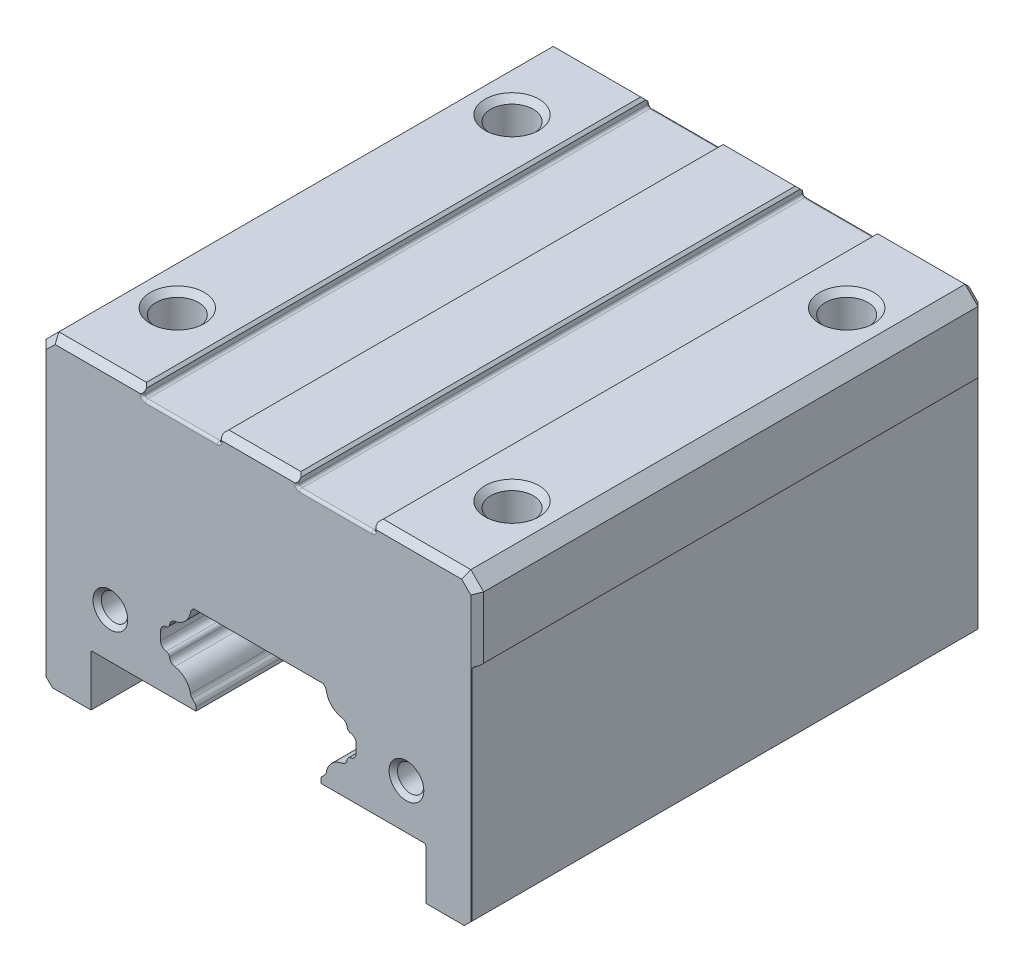
SolidWorks part; units mm, degrees
material "Plain Carbon Steel"
ref_plane "Front Plane" through (0, 0, 0) normal (0, 0, 1) x (1, 0, 0)
ref_plane "Top Plane" through (0, 0, 0) normal (0, 1, 0) x (1, 0, 0)
ref_plane "Right Plane" through (0, 0, 0) normal (1, 0, 0) x (0, 0, -1)
sketch "Rail Profile" plane through (0, 0, 0) normal (0, 0, 1) x (1, 0, 0)
  line L47 (0, 0) -> (0, 28) construction
  line L48 (-7, 0) -> (7, 0)
  line L49 (7, 0) -> (7.5, 0.5)
  line L50 (7.5, 0.5) -> (7.5, 3.0858)
  line L58 (7.2071, 3.7929) -> (4.8672, 6.1328)
  line L59 (4.75, 6.4157) -> (4.75, 8.5843)
  line L60 (4.8672, 8.8672) -> (5.063, 9.063)
  line L61 (7.5, 11.6657) -> (7.5, 12.3343)
  line L62 (-7, 0) -> (-7.5, 0.5)
  line L63 (5, 15) -> (-5, 15)
  line L64 (6.75, 9) -> (6.75, 15) construction
  line L65 (5.063, 14.937) -> (5, 15)
  line L66 (-7.5, 0.5) -> (-7.5, 3.0858)
  line L67 (6.75, 15) -> (3.75, 12) construction
  line L68 (3.75, 12) -> (6.75, 9) construction
  line L69 (7.1, 12.3343) -> (7.1, 11.6657) construction
  line L70 (6.4042, 13.0301) -> (6.4042, 10.9699) construction
  line L71 (-7.2071, 3.7929) -> (-4.8672, 6.1328)
  line L72 (-4.75, 6.4157) -> (-4.75, 8.5843)
  line L73 (-4.8672, 8.8672) -> (-5.063, 9.063)
  line L74 (5, 15) -> (8, 12) construction
  line L75 (4.8672, 8.8672) -> (8, 12) construction
  line L76 (-7.5, 11.6657) -> (-7.5, 12.3343)
  line L77 (-5.063, 14.937) -> (-5, 15)
  arc A4 (6.4734, 13.4241) -> (5.1741, 14.7234) centre (6.75, 15) cw
  arc A6 (5.1741, 9.2766) -> (6.4734, 10.5759) centre (6.75, 9) cw
  arc A7 (7.2071, 3.7929) -> (7.5, 3.0858) centre (6.5, 3.0858) cw
  arc A8 (5.063, 14.937) -> (5.1741, 14.7234) centre (4.7801, 14.6542) cw
  arc A9 (6.4734, 13.4241) -> (6.8012, 13.0792) centre (6.4042, 13.0301) cw
  arc A10 (7.1491, 12.7313) -> (7.5, 12.3343) centre (7.1, 12.3343) cw
  arc A11 (7.5, 11.6657) -> (7.1491, 11.2687) centre (7.1, 11.6657) cw
  arc A12 (6.8012, 10.9208) -> (6.4734, 10.5759) centre (6.4042, 10.9699) cw
  arc A13 (5.1741, 9.2766) -> (5.063, 9.063) centre (4.7801, 9.3458) cw
  arc A14 (4.8672, 8.8672) -> (4.75, 8.5843) centre (5.15, 8.5843) ccw
  arc A15 (4.75, 6.4157) -> (4.8672, 6.1328) centre (5.15, 6.4157) ccw
  arc A16 (6.8012, 13.0792) -> (7.1491, 12.7313) centre (7.1981, 13.1283) ccw
  arc A17 (7.1491, 11.2687) -> (6.8012, 10.9208) centre (7.1981, 10.8717) ccw
  arc A18 (-7.2071, 3.7929) -> (-7.5, 3.0858) centre (-6.5, 3.0858) ccw
  arc A19 (-4.75, 6.4157) -> (-4.8672, 6.1328) centre (-5.15, 6.4157) cw
  arc A20 (-4.8672, 8.8672) -> (-4.75, 8.5843) centre (-5.15, 8.5843) cw
  arc A21 (-5.1741, 9.2766) -> (-5.063, 9.063) centre (-4.7801, 9.3458) ccw
  arc A22 (-5.1741, 9.2766) -> (-6.4734, 10.5759) centre (-6.75, 9) ccw
  arc A23 (-6.8012, 10.9208) -> (-6.4734, 10.5759) centre (-6.4042, 10.9699) ccw
  arc A24 (-7.1491, 11.2687) -> (-6.8012, 10.9208) centre (-7.1981, 10.8717) cw
  arc A25 (-7.5, 11.6657) -> (-7.1491, 11.2687) centre (-7.1, 11.6657) ccw
  arc A26 (-7.1491, 12.7313) -> (-7.5, 12.3343) centre (-7.1, 12.3343) ccw
  arc A27 (-6.8012, 13.0792) -> (-7.1491, 12.7313) centre (-7.1981, 13.1283) cw
  arc A28 (-6.4734, 13.4241) -> (-6.8012, 13.0792) centre (-6.4042, 13.0301) ccw
  arc A29 (-6.4734, 13.4241) -> (-5.1741, 14.7234) centre (-6.75, 15) ccw
  arc A30 (-5.063, 14.937) -> (-5.1741, 14.7234) centre (-4.7801, 14.6542) ccw
  point P2 (4.75, 7.5)
  point P12 (7.5, 12)
  point P19 (6.75, 12)
  point P25 (5.1578, 14.8422)
  point P50 (8, 12)
  point P78 (0, 15)
  dimension "Rb" = 1.6
  dimension "Rf1" = 1
  dimension "Rf2" = 0.4
  dimension "WR" = 15
  dimension "Wi" = 9.5
  dimension "Wt" = 5
  dimension "Ac" = 135
  dimension "HR" = 15
  dimension "Hm" = 7.5
  dimension "Hb" = 12
  dimension "Hc" = 0.5
  dimension "Wb" = 7.5
sketch "Block Profile" plane through (0, 0, 0) normal (0, 0, 1) x (1, 0, 0)
  line L16 (16, 4.3) -> (13, 4.3)
  line L17 (0, 0) -> (0, 28) construction
  line L18 (17, 5.3) -> (17, 27)
  line L19 (16, 28) -> (-16, 28)
  line L20 (5.0414, 15.1) -> (-5.0414, 15.1)
  line L21 (0, 15.1) -> (0, 28) construction
  line L22 (17, 5.3) -> (16, 4.3)
  line L23 (17, 27) -> (16, 28)
  line L24 (13, 4.3) -> (13, 8.2)
  line L25 (12.9, 8.3) -> (4.85, 8.3)
  line L26 (-5.1337, 15.0077) -> (-5.0414, 15.1)
  line L27 (-7.6, 11.6657) -> (-7.6, 12.3343)
  line L28 (-4.9379, 8.7964) -> (-5.1337, 8.9923)
  line L29 (-4.85, 8.3) -> (-4.85, 8.5843)
  line L30 (-12.9, 8.3) -> (-4.85, 8.3)
  line L31 (-13, 4.3) -> (-13, 8.2)
  line L32 (5.0414, 15.1) -> (-5.0414, 15.1)
  line L33 (-5.0414, 15.1) -> (-5.1337, 15.0077)
  line L34 (-7.6, 12.3343) -> (-7.6, 11.6657)
  line L35 (-5.1337, 8.9923) -> (-4.9379, 8.7964)
  line L36 (-4.85, 8.5843) -> (-4.85, 6.4157)
  line L37 (-4.9379, 6.2036) -> (-7.2778, 3.8636)
  line L38 (-7.6, 3.0858) -> (-7.6, 0.4586)
  line L39 (-7.6, 0.4586) -> (-7.0414, -0.1)
  line L40 (-7.0414, -0.1) -> (7.0414, -0.1)
  line L41 (7.0414, -0.1) -> (7.6, 0.4586)
  line L42 (7.6, 0.4586) -> (7.6, 3.0858)
  line L43 (7.2778, 3.8636) -> (4.9379, 6.2036)
  line L44 (4.85, 6.4157) -> (4.85, 8.5843)
  line L45 (4.9379, 8.7964) -> (5.1337, 8.9923)
  line L46 (7.6, 11.6657) -> (7.6, 12.3343)
  line L47 (5.1337, 15.0077) -> (5.0414, 15.1)
  line L60 (4.85, 8.3) -> (4.85, 8.5843)
  line L61 (4.9379, 8.7964) -> (5.1337, 8.9923)
  line L62 (7.6, 11.6657) -> (7.6, 12.3343)
  line L63 (5.1337, 15.0077) -> (5.0414, 15.1)
  line L64 (-16, 4.3) -> (-13, 4.3)
  line L65 (-17, 5.3) -> (-16, 4.3)
  line L66 (-17, 5.3) -> (-17, 27)
  line L67 (-17, 27) -> (-16, 28)
  arc A26 (12.9, 8.3) -> (13, 8.2) centre (12.9, 8.2) cw
  arc A27 (-5.2726, 14.7406) -> (-5.1337, 15.0077) centre (-4.7801, 14.6542) cw
  arc A28 (-5.2726, 14.7406) -> (-6.4906, 13.5226) centre (-6.75, 15) cw
  arc A29 (-6.9004, 13.0915) -> (-6.4906, 13.5226) centre (-6.4042, 13.0301) cw
  arc A30 (-6.9004, 13.0915) -> (-7.1613, 12.8305) centre (-7.1981, 13.1283) cw
  arc A31 (-7.6, 12.3343) -> (-7.1613, 12.8305) centre (-7.1, 12.3343) cw
  arc A32 (-7.1613, 11.1695) -> (-7.6, 11.6657) centre (-7.1, 11.6657) cw
  arc A33 (-7.1613, 11.1695) -> (-6.9004, 10.9085) centre (-7.1981, 10.8717) cw
  arc A34 (-6.4906, 10.4774) -> (-6.9004, 10.9085) centre (-6.4042, 10.9699) cw
  arc A35 (-6.4906, 10.4774) -> (-5.2726, 9.2594) centre (-6.75, 9) cw
  arc A36 (-5.1337, 8.9923) -> (-5.2726, 9.2594) centre (-4.7801, 9.3458) cw
  arc A37 (-4.9379, 8.7964) -> (-4.85, 8.5843) centre (-5.15, 8.5843) cw
  arc A38 (-12.9, 8.3) -> (-13, 8.2) centre (-12.9, 8.2) ccw
  arc A52 (-5.1337, 15.0077) -> (-5.2726, 14.7406) centre (-4.7801, 14.6542) ccw
  arc A53 (-6.4906, 13.5226) -> (-5.2726, 14.7406) centre (-6.75, 15) ccw
  arc A54 (-6.4906, 13.5226) -> (-6.9004, 13.0915) centre (-6.4042, 13.0301) ccw
  arc A55 (-7.1613, 12.8305) -> (-6.9004, 13.0915) centre (-7.1981, 13.1283) ccw
  arc A56 (-7.1613, 12.8305) -> (-7.6, 12.3343) centre (-7.1, 12.3343) ccw
  arc A57 (-7.6, 11.6657) -> (-7.1613, 11.1695) centre (-7.1, 11.6657) ccw
  arc A58 (-6.9004, 10.9085) -> (-7.1613, 11.1695) centre (-7.1981, 10.8717) ccw
  arc A59 (-6.9004, 10.9085) -> (-6.4906, 10.4774) centre (-6.4042, 10.9699) ccw
  arc A60 (-5.2726, 9.2594) -> (-6.4906, 10.4774) centre (-6.75, 9) ccw
  arc A61 (-5.2726, 9.2594) -> (-5.1337, 8.9923) centre (-4.7801, 9.3458) ccw
  arc A62 (-4.85, 8.5843) -> (-4.9379, 8.7964) centre (-5.15, 8.5843) ccw
  arc A63 (-4.9379, 6.2036) -> (-4.85, 6.4157) centre (-5.15, 6.4157) ccw
  arc A64 (-7.2778, 3.8636) -> (-7.6, 3.0858) centre (-6.5, 3.0858) ccw
  arc A65 (7.6, 3.0858) -> (7.2778, 3.8636) centre (6.5, 3.0858) ccw
  arc A66 (4.85, 6.4157) -> (4.9379, 6.2036) centre (5.15, 6.4157) ccw
  arc A67 (4.9379, 8.7964) -> (4.85, 8.5843) centre (5.15, 8.5843) ccw
  arc A68 (5.1337, 8.9923) -> (5.2726, 9.2594) centre (4.7801, 9.3458) ccw
  arc A69 (6.4906, 10.4774) -> (5.2726, 9.2594) centre (6.75, 9) ccw
  arc A70 (6.4906, 10.4774) -> (6.9004, 10.9085) centre (6.4042, 10.9699) ccw
  arc A71 (7.1613, 11.1695) -> (6.9004, 10.9085) centre (7.1981, 10.8717) ccw
  arc A72 (7.1613, 11.1695) -> (7.6, 11.6657) centre (7.1, 11.6657) ccw
  arc A73 (7.6, 12.3343) -> (7.1613, 12.8305) centre (7.1, 12.3343) ccw
  arc A74 (6.9004, 13.0915) -> (7.1613, 12.8305) centre (7.1981, 13.1283) ccw
  arc A75 (6.9004, 13.0915) -> (6.4906, 13.5226) centre (6.4042, 13.0301) ccw
  arc A76 (5.2726, 14.7406) -> (6.4906, 13.5226) centre (6.75, 15) ccw
  arc A77 (5.2726, 14.7406) -> (5.1337, 15.0077) centre (4.7801, 14.6542) ccw
  arc A93 (4.9379, 8.7964) -> (4.85, 8.5843) centre (5.15, 8.5843) ccw
  arc A94 (5.1337, 8.9923) -> (5.2726, 9.2594) centre (4.7801, 9.3458) ccw
  arc A95 (6.4906, 10.4774) -> (5.2726, 9.2594) centre (6.75, 9) ccw
  arc A96 (6.4906, 10.4774) -> (6.9004, 10.9085) centre (6.4042, 10.9699) ccw
  arc A97 (7.1613, 11.1695) -> (6.9004, 10.9085) centre (7.1981, 10.8717) ccw
  arc A98 (7.1613, 11.1695) -> (7.6, 11.6657) centre (7.1, 11.6657) ccw
  arc A99 (7.6, 12.3343) -> (7.1613, 12.8305) centre (7.1, 12.3343) ccw
  arc A100 (6.9004, 13.0915) -> (7.1613, 12.8305) centre (7.1981, 13.1283) ccw
  arc A101 (6.9004, 13.0915) -> (6.4906, 13.5226) centre (6.4042, 13.0301) ccw
  arc A102 (5.2726, 14.7406) -> (6.4906, 13.5226) centre (6.75, 15) ccw
  arc A103 (5.2726, 14.7406) -> (5.1337, 15.0077) centre (4.7801, 14.6542) ccw
  point P0 (17, 4.3)
  point P5 (17, 28)
  point P15 (13, 8.3)
  dimension "D9" = 0.1
  dimension "D2" = 4.3
  dimension "D3" = 17
  dimension "D4" = 23.7
  dimension "D5" = 4
  dimension "D6" = 13
  dimension "D1" = 0.1
extrude "Block Body" add sketch "Block Profile" along normal mid plane 39.4
sketch "Side Reference Sketch" plane through (17, 0, 0) normal (1, 0, 0) x (0, 0, -1)
  line L0 (0, 0) -> (0, 28) construction
  line L1 (-20, 22) -> (20, 22)
  line L2 (-20, 22) -> (-20, 2)
  line L3 (-20, 2) -> (20, 2)
  line L4 (20, 22) -> (20, 2)
  line L5 (-20, 22) -> (20, 2) construction
  line L6 (-20, 2) -> (20, 22) construction
  line L7 (-19.7, 28) -> (19.7, 28) construction
  point P0 (0, 12)
  dimension "D1" = 20
  dimension "D2" = 40
  dimension "D3" = 6
extrude "Side Reference" cut sketch "Side Reference Sketch" against normal blind 0.45
chamfer "Aesthetic Chamfer 1" distance 0.5 angle 45 10 edges at (-17, 16.15, -19.7) (-16.5, 27.5, -19.7) (0, 28, -19.7) (16.5, 27.5, -19.7) (17, 24.5, -19.7) (-17, 16.15, 19.7) (-16.5, 27.5, 19.7) (17, 24.5, 19.7) (16.5, 27.5, 19.7) (0, 28, 19.7)
sketch "Casting Groove Sketch" plane through (0, 28, 0) normal (0, 1, 0) x (1, 0, 0)
  line L0 (-6, 0) -> (6, 0) construction
  line L1 (-9, 20) -> (-3, 20)
  line L2 (-9, 20) -> (-9, -20)
  line L3 (-9, -20) -> (-3, -20)
  line L4 (-3, 20) -> (-3, -20)
  line L5 (-9, 20) -> (-3, -20) construction
  line L6 (-9, -20) -> (-3, 20) construction
  line L7 (3, 20) -> (9, 20)
  line L8 (3, 20) -> (3, -20)
  line L9 (3, -20) -> (9, -20)
  line L10 (9, 20) -> (9, -20)
  line L11 (3, 20) -> (9, -20) construction
  line L12 (3, -20) -> (9, 20) construction
  point P0 (-6, 0)
  point P5 (6, 0)
  point P12 (0, 0)
  dimension "D1" = 40
  dimension "D2" = 6
  dimension "D3" = 40
  dimension "D4" = 6
  dimension "D5" = 12
extrude "Casting Goorve" cut sketch "Casting Groove Sketch" against normal blind 0.75
chamfer "Aesthetic Chamfer 2" distance 0.2 angle 45 1 edges at (17, 22, 0)
fillet "Production Fillet" radius 0.2 17 edges at (3, 27.375, -19.7) (3, 27.375, 19.7) (9, 27.375, -19.7) (9, 27.375, 19.7) (-9, 27.375, -19.7) (-9, 27.375, 19.7) (-3, 27.375, -19.7) (-3, 27.375, 19.7) (3, 27.25, 0) (6, 27.25, -19.7) (9, 27.25, 0) (6, 27.25, 19.7) (-9, 27.25, 0) (-6, 27.25, -19.7) (-3, 27.25, 0) (-6, 27.25, 19.7) (16.55, 22, 0)
hole_wizard "Fixing Holes" positions "Sketch4" profile "Sketch5" tap size "M4" standard "ISO"
sketch "Sketch4" plane through (0, 28, 0) normal (0, 1, 0) x (1, 0, 0)
  line L1 (-13, -13) -> (13, -13) construction
  line L2 (-13, -13) -> (-13, 13) construction
  line L3 (-13, 13) -> (13, 13) construction
  line L4 (13, -13) -> (13, 13) construction
  line L5 (-13, -13) -> (13, 13) construction
  line L6 (-13, 13) -> (13, -13) construction
  line L7 (17, -19.2) -> (17, 19.2) construction
  line L9 (-9.2, -19.7) -> (-15.7929, -19.7) construction
  point P0 (-13, -13)
  point P2 (-13, 13)
  point P4 (13, 13)
  point P6 (13, -13)
  point P32 (0, 0)
  dimension "D1" = 26
  dimension "D2" = 4
  dimension "D3" = 19.7
sketch "Sketch5" plane through (-13, 28, 13) normal (1, 0, 0) x (0, 0, 1)
  line L0 (0, 0) -> (0, 8.0914)
  line L1 (0, 8.0914) -> (1.65, 7.1)
  line L2 (1.65, 7.1) -> (1.65, 0.45)
  line L3 (1.65, 0.45) -> (2.1, 0)
  line L5 (2.1, 0) -> (0, 0)
  line L6 (-1.65, 0.45) -> (-2.1, 0) construction
  line L10 (0, 8.0914) -> (-1.65, 7.1) construction
  line L11 (0, -6.35) -> (0, 107.95) construction
  dimension "Tap Drill Dia." = 3.3
  dimension "Tap Drill Depth" = 7.1
  dimension "Near C'Sink Dia." = 4.2
  dimension "Near C'Sink Angle" = 90
  dimension "Drill Angle" = 118
cosmetic thread "Hole Thread1" parameters "D1"=5, "D2"=4
cosmetic thread "Hole Thread2" parameters "D1"=5, "D2"=4
cosmetic thread "Hole Thread3" parameters "D1"=5, "D2"=4
cosmetic thread "Hole Thread4" parameters "D1"=5, "D2"=4
hole_wizard "End Cap Fixing Holes Front" positions "Sketch6" profile "Sketch7" tap size "M2.5" standard "ISO"
sketch "Sketch6" plane through (0, 0, 19.7) normal (0, 0, 1) x (1, 0, 0)
  line L0 (11.5, 11.8) -> (-11.5, 11.8) construction
  line L2 (0, 0) -> (0, 28) construction
  line L5 (13, 4.3) -> (16, 4.3) construction
  point P0 (-11.5, 11.8)
  point P2 (11.5, 11.8)
  point P9 (0, 11.8)
  dimension "D1" = 23
  dimension "D2" = 7.5
sketch "Sketch7" plane through (-11.5, 11.8, 19.7) normal (1, 0, 0) x (0, -1, 0)
  line L0 (0, 0) -> (0, 6.9659)
  line L1 (0, 6.9659) -> (1.025, 6.35)
  line L2 (1.025, 6.35) -> (1.025, 0.325)
  line L3 (1.025, 0.325) -> (1.35, 0)
  line L5 (1.35, 0) -> (0, 0)
  line L6 (-1.025, 0.325) -> (-1.35, 0) construction
  line L10 (0, 6.9659) -> (-1.025, 6.35) construction
  line L11 (0, -6.35) -> (0, 107.95) construction
  dimension "Tap Drill Dia." = 2.05
  dimension "Tap Drill Depth" = 6.35
  dimension "Near C'Sink Dia." = 2.7
  dimension "Near C'Sink Angle" = 90
  dimension "Drill Angle" = 118
cosmetic thread "Hole Thread5" parameters "D1"=5, "D2"=2.5
cosmetic thread "Hole Thread6" parameters "D1"=5, "D2"=2.5
hole_wizard "End Cap Fixing Holes Back" positions "Sketch9" profile "Sketch10" tap size "M2.5" standard "ISO"
sketch "Sketch9" plane through (0, 0, -19.7) normal (0, 0, -1) x (-1, 0, 0)
  line L0 (-11.5, 11.8) -> (11.5, 11.8) construction
  line L2 (2.8, 27.5) -> (-2.8, 27.5) construction
  line L4 (-13, 4.3) -> (-16, 4.3) construction
  point P0 (-11.5, 11.8)
  point P2 (11.5, 11.8)
  point P9 (0, 11.8)
  point P12 (0, 27.5)
  dimension "D1" = 23
  dimension "D2" = 7.5
sketch "Sketch10" plane through (11.5, 11.8, -19.7) normal (1, 0, 0) x (0, 1, 0)
  line L0 (0, 0) -> (0, 6.9659)
  line L1 (0, 6.9659) -> (1.025, 6.35)
  line L2 (1.025, 6.35) -> (1.025, 0.325)
  line L3 (1.025, 0.325) -> (1.35, 0)
  line L5 (1.35, 0) -> (0, 0)
  line L6 (-1.025, 0.325) -> (-1.35, 0) construction
  line L10 (0, 6.9659) -> (-1.025, 6.35) construction
  line L11 (0, -6.35) -> (0, 107.95) construction
  dimension "Tap Drill Dia." = 2.05
  dimension "Tap Drill Depth" = 6.35
  dimension "Near C'Sink Dia." = 2.7
  dimension "Near C'Sink Angle" = 90
  dimension "Drill Angle" = 118
cosmetic thread "Hole Thread8" parameters "D1"=5, "D2"=2.5
cosmetic thread "Hole Thread9" parameters "D1"=5, "D2"=2.5
equation "\"Wt@Rail Profile\"= \"WR@Rail Profile\" / 3'Top Side Half Width"
equation "\"Hm@Rail Profile\"= \"HR@Rail Profile\" / 2'Recirculation Avoidance Height"
equation "\"Hb@Rail Profile\"= 0.8 * \"HR@Rail Profile\"'Pivot Height"
equation "\"Hc@Rail Profile\"= \"WR@Rail Profile\" / 30'Chamfer Width"
equation "\"Wb@Rail Profile\"= \"WR@Rail Profile\" / 2'Ball Center Cross Width"
